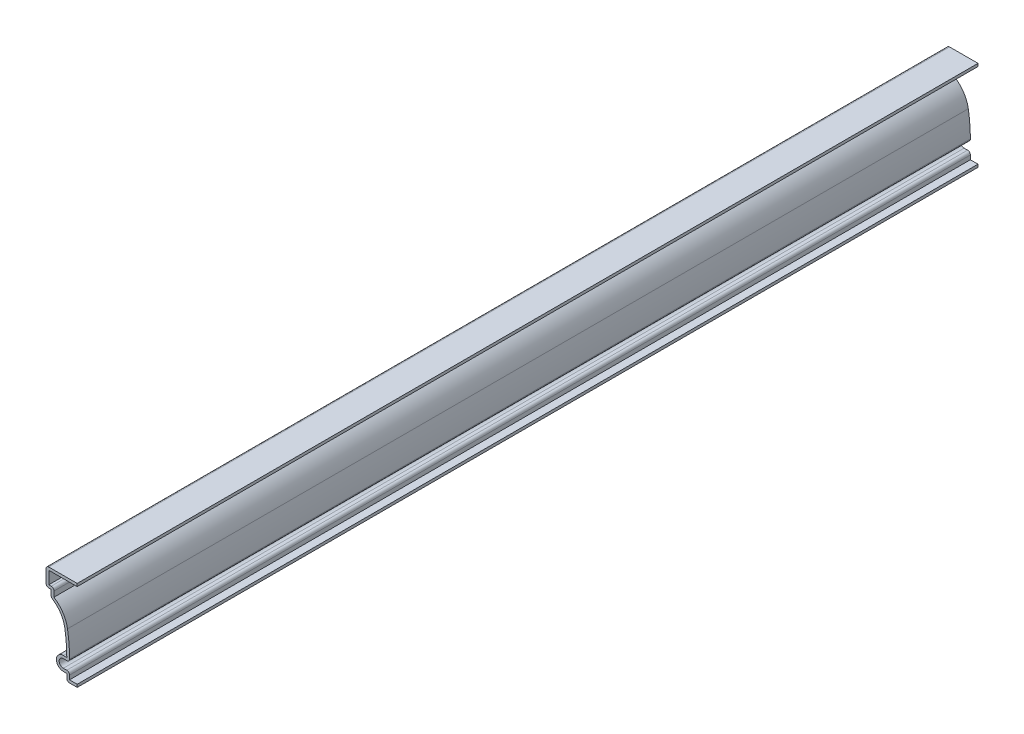
SolidWorks part; units mm, degrees
ref_plane "Front Plane" through (0, 0, 0) normal (0, 0, 1) x (1, 0, 0)
ref_plane "Top Plane" through (0, 0, 0) normal (0, 1, 0) x (1, 0, 0)
ref_plane "Right Plane" through (0, 0, 0) normal (1, 0, 0) x (0, 0, -1)
sketch "Sketch1" plane through (0, 0, 0) normal (0, 0, 1) x (1, 0, 0)
  line L0 (0, 0) -> (0, 41.275) construction
  line L1 (0, 41.275) -> (-14.2875, 41.275)
  line L2 (-14.2875, 41.275) -> (-14.2875, 32.9406)
  line L3 (-14.2875, 32.9406) -> (-11.9062, 32.9406)
  line L4 (-11.9062, 32.9406) -> (-11.9062, 29.7656)
  line L5 (0, 0) -> (-4.7625, 0)
  line L6 (-4.7625, 0) -> (-4.7625, 3.175)
  line L7 (-4.7625, 3.175) -> (-6.35, 3.175)
  line L8 (-6.35, 9.525) -> (-4.7625, 9.525)
  line L9 (-4.7625, 9.525) -> (-4.7625, 35.3054) construction
  line L10 (-14.2875, 32.9406) -> (-14.2875, 15.3572) construction
  arc A0 (-11.9062, 29.7656) -> (-5.6935, 20.8259) centre (-18.2222, 18.7475) cw
  arc A1 (-6.35, 3.175) -> (-6.35, 9.525) centre (-6.35, 6.35) cw
  arc A2 (-5.6935, 20.8259) -> (-4.7625, 9.525) centre (-73.8188, 9.525) cw
  point P15 (-5.6967, 20.8331)
  dimension "D1" = 3.175
  dimension "D4" = 12.7
  dimension "D11" = 69.0563
  dimension "D2" = 3.175
  dimension "D3" = 4.7625
  dimension "D5" = 2.3813
  dimension "D6" = 3.175
  dimension "D7" = 8.3344
  dimension "D8" = 14.2875
  dimension "D9" = 41.275
  dimension "D10" = 1.5875
extrude "Extrude-Thin1" add sketch "Sketch1" against normal blind 412.75 thin thin type one direction reverse wall 1.27
fillet "Fillet1" radius 1.27 7 edges at (-4.7625, 0, -206.375) (-3.4925, 4.445, -206.375) (-3.504, 8.255, -206.375) (-11.9062, 29.7656, -206.375) (-14.2875, 32.9406, -206.375) (-10.6362, 34.2106, -206.375) (-14.2875, 41.275, -206.375)
